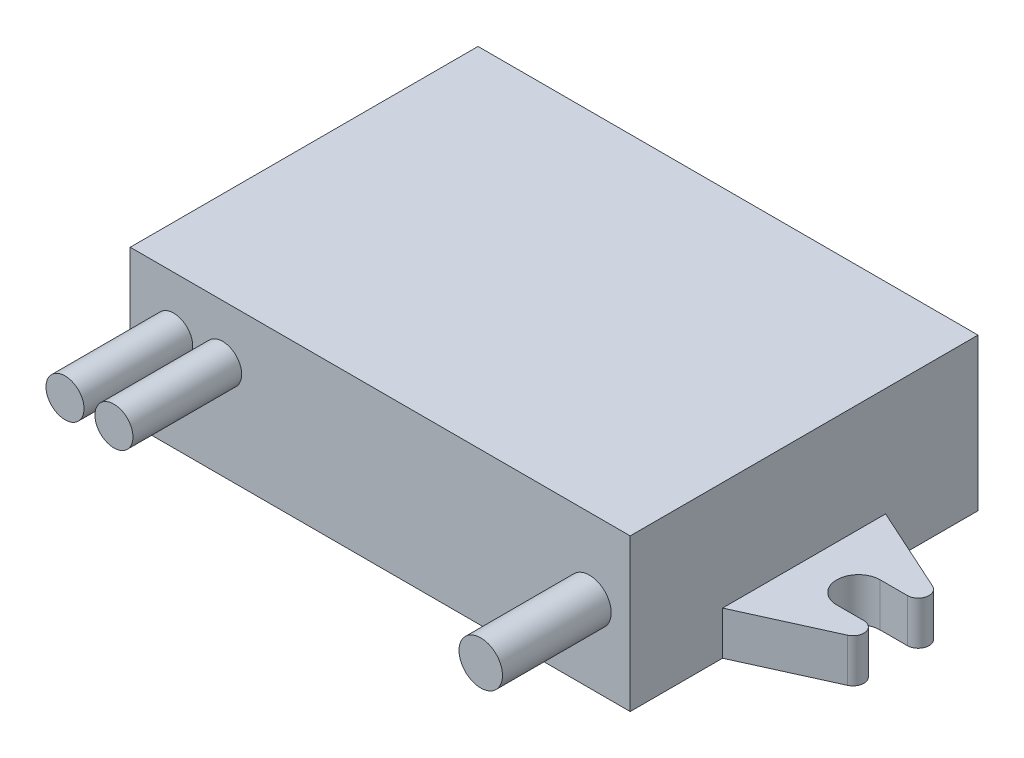
SolidWorks part; units mm, degrees
ref_plane "Front Plane" through (0, 0, 0) normal (0, 0, 1) x (1, 0, 0)
ref_plane "Top Plane" through (0, 0, 0) normal (0, 1, 0) x (1, 0, 0)
ref_plane "Right Plane" through (0, 0, 0) normal (1, 0, 0) x (0, 0, -1)
sketch "Sketch1" plane through (0, 0, 0) normal (0, 1, 0) x (1, 0, 0)
  line L1 (-23, -16) -> (23, -16)
  line L2 (-23, -16) -> (-23, 16)
  line L3 (-23, 16) -> (23, 16)
  line L4 (23, -16) -> (23, 16)
  line L5 (-23, -16) -> (23, 16) construction
  line L6 (-23, 16) -> (23, -16) construction
  point P0 (0, 0)
  dimension "D1" = 46
  dimension "D2" = 32
extrude "Boss-Extrude1" add sketch "Sketch1" along normal blind 14 contours L2 L3 L4 L1
sketch "Sketch2" plane through (0, 0, 0) normal (0, -1, 0) x (1, 0, 0)
  line L0 (-23, 0) -> (0, 0) construction
  line L1 (-23, 16) -> (-23, -16) construction
  line L2 (-23, 0) -> (-28, 0) construction
  line L3 (-28, 2) -> (-30.5, 2)
  line L4 (-30.9131, 3.9107) -> (-23, 7.5)
  line L5 (-23, 7.5) -> (-23, 0)
  line L6 (-23, 0) -> (-26, 0)
  line L7 (0, 0) -> (0, 16) construction
  line L8 (-23, 16) -> (23, 16) construction
  arc A0 (-26, 0) -> (-28, 2) centre (-28, 0) ccw
  arc A1 (-30.5, 2) -> (-30.9131, 3.9107) centre (-30.5, 3) cw
  dimension "D1" = 2
  dimension "D5" = 1
  dimension "D2" = 28
  dimension "D3" = 7.5
  dimension "D4" = 31.5
extrude "Boss-Extrude2" add sketch "Sketch2" against normal blind 4
mirror "Mirror1" about plane through (0, 0, 0) normal (0, 0, 1) of "Boss-Extrude2"
mirror "Mirror2" about plane through (0, 0, 0) normal (1, 0, 0) of "Mirror1", "Boss-Extrude2"
sketch "Sketch3" plane through (0, 0, 16) normal (0, 0, 1) x (1, 0, 0)
  line L0 (-23, 0) -> (23, 0) construction
  line L1 (23, 14) -> (15.5, 14) construction
  line L2 (23, 14) -> (23, 0) construction
  line L3 (23, 0) -> (15.5, 0) construction
  line L4 (15.5, 14) -> (15.5, 0) construction
  line L5 (15.5, 0) -> (23, 14) construction
  line L6 (-23, 14) -> (23, 14) construction
  line L7 (-23, 4) -> (-10.5, 4) construction
  line L8 (-23, 4) -> (-23, 14) construction
  line L9 (-23, 14) -> (-10.5, 14) construction
  line L10 (-10.5, 4) -> (-10.5, 14) construction
  line L11 (-10.5, 9) -> (-23, 9) construction
  line L12 (-14.5, 9) -> (-10.5, 14) construction
  line L13 (-19, 9) -> (-23, 4) construction
  circle A0 centre (-19, 9) radius 1.75
  circle A1 centre (-14.5, 9) radius 1.75
  circle A2 centre (19.25, 7) radius 2
  dimension "D1" = 3.5
  dimension "D3" = 4
  dimension "D2" = 4.5
  dimension "D4" = 12.5
  dimension "D5" = 7.5
extrude "Boss-Extrude3" add sketch "Sketch3" along normal blind 10
